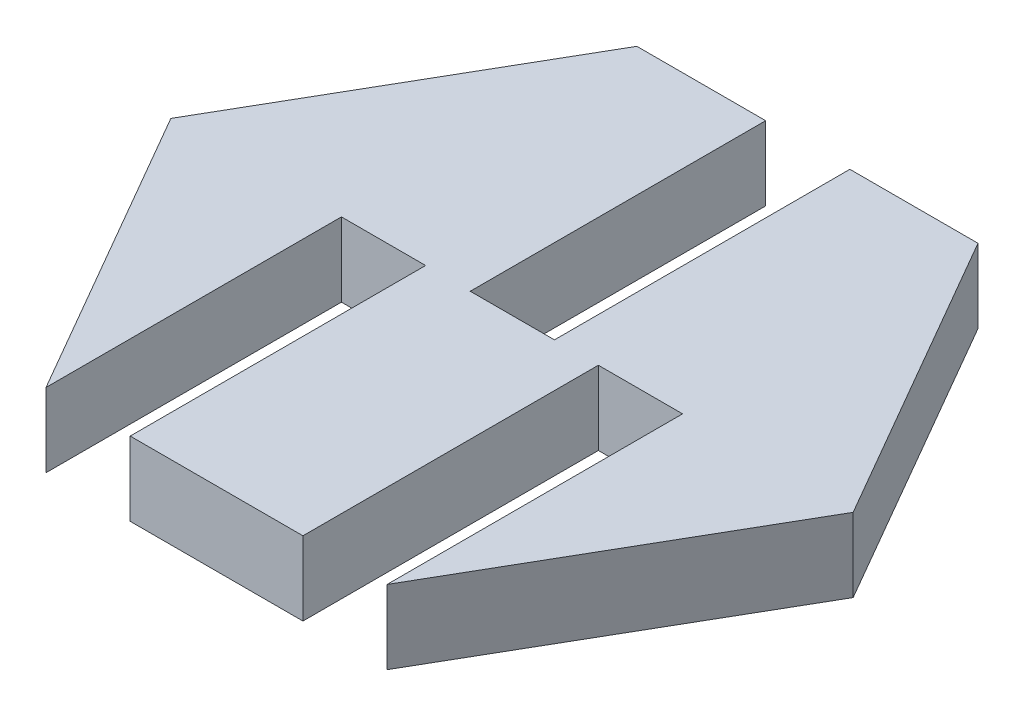
SolidWorks part; units mm, degrees
ref_plane "Front Plane" through (0, 0, 0) normal (0, 0, 1) x (1, 0, 0)
ref_plane "Top Plane" through (0, 0, 0) normal (0, 1, 0) x (1, 0, 0)
ref_plane "Right Plane" through (0, 0, 0) normal (1, 0, 0) x (0, 0, -1)
sketch "Sketch1" plane through (0, 0, 0) normal (0, 1, 0) x (1, 0, 0)
  line L1 (11.547, 0) -> (5.7735, 10)
  line L2 (5.7735, 10) -> (-5.7735, 10)
  line L3 (-5.7735, 10) -> (-11.547, 0)
  line L4 (-11.547, 0) -> (-5.7735, -10)
  line L5 (-5.7735, -10) -> (5.7735, -10)
  line L6 (5.7735, -10) -> (11.547, 0)
  circle A0 centre (0, 0) radius 10 construction
  dimension "D1" = 20
extrude "Boss-Extrude1" add sketch "Sketch1" along normal blind 2.5
sketch "Sketch5" plane through (0, 0, 10) normal (0, 0, 1) x (1, 0, 0)
  line L0 (-5.7735, 0) -> (5.7735, 0) construction
  line L1 (-5.7735, 2.5) -> (-2.9235, 2.5)
  line L2 (-5.7735, 2.5) -> (-5.7735, 0)
  line L3 (-5.7735, 0) -> (-2.9235, 0)
  line L4 (-2.9235, 2.5) -> (-2.9235, 0)
  dimension "D1" = 2.85
extrude "Cut-Extrude3" cut sketch "Sketch5" against normal blind 10
sketch "Sketch6" plane through (0, 0, 10) normal (0, 0, 1) x (1, 0, 0)
  line L0 (-2.9235, 0) -> (5.7735, 0) construction
  line L1 (5.7735, 2.5) -> (2.9235, 2.5)
  line L2 (5.7735, 2.5) -> (5.7735, 0)
  line L3 (5.7735, 0) -> (2.9235, 0)
  line L4 (2.9235, 2.5) -> (2.9235, 0)
  dimension "D1" = 2.85
extrude "Cut-Extrude4" cut sketch "Sketch6" against normal blind 10
sketch "Sketch7" plane through (0, 0, -10) normal (0, 0, -1) x (-1, 0, 0)
  line L0 (-5.7735, 2.5) -> (5.7735, 2.5) construction
  line L1 (1.4135, 2.5) -> (-1.4365, 2.5)
  line L2 (1.4135, 2.5) -> (1.4135, 0)
  line L3 (1.4135, 0) -> (-1.4365, 0)
  line L4 (-1.4365, 2.5) -> (-1.4365, 0)
  line L5 (-5.7735, 0) -> (5.7735, 0) construction
  line L6 (5.7735, 2.5) -> (5.7735, 0) construction
  dimension "D1" = 2.85
  dimension "D2" = 4.36
extrude "Cut-Extrude5" cut sketch "Sketch7" against normal blind 10
